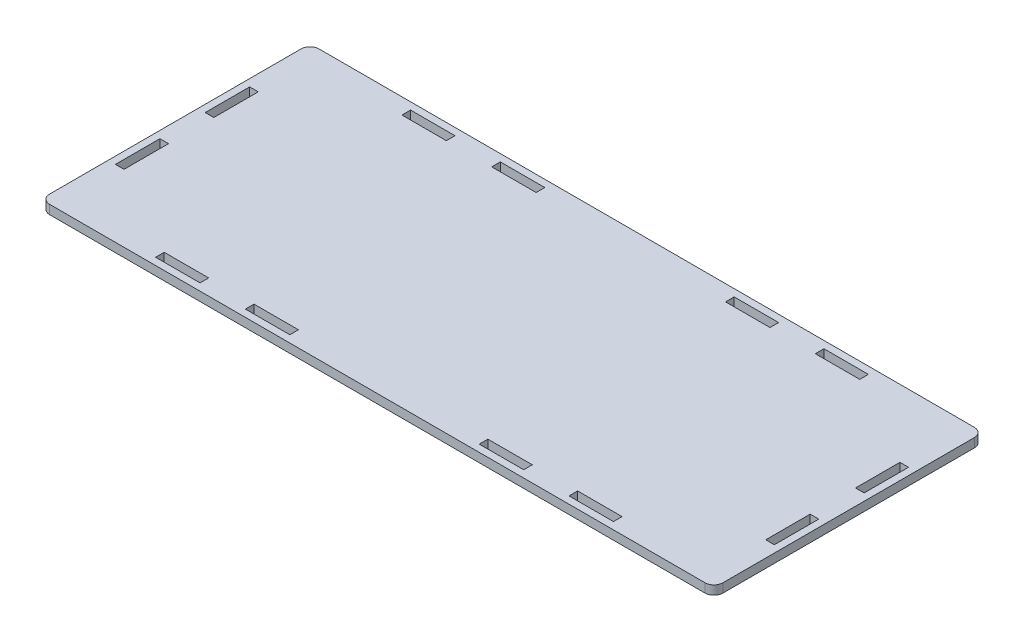
SolidWorks part; units mm, degrees
ref_plane "Front Plane" through (0, 0, 0) normal (0, 0, 1) x (1, 0, 0)
ref_plane "Top Plane" through (0, 0, 0) normal (0, 1, 0) x (1, 0, 0)
ref_plane "Right Plane" through (0, 0, 0) normal (1, 0, 0) x (0, 0, -1)
sketch "Sketch1" plane through (0, 0, 0) normal (0, 1, 0) x (1, 0, 0)
  line L1 (0, 0) -> (750, 0)
  line L2 (0, 0) -> (0, 300)
  line L3 (0, 300) -> (750, 300)
  line L4 (750, 0) -> (750, 300)
  dimension "D1" = 750
  dimension "D2" = 300
extrude "Boss-Extrude1" add sketch "Sketch1" along normal blind 10 contours L3 L4 L1 L2
sketch "Sketch2" plane through (0, 10, 0) normal (0, 1, 0) x (1, 0, 0)
  line L0 (375, 300) -> (375, 0) construction
  line L1 (0, 300) -> (750, 300) construction
  line L2 (0, 0) -> (750, 0) construction
  line L3 (375, 150) -> (585, 150) construction
  line L4 (585, 80) -> (585, 220) construction
  line L5 (655, 80) -> (585, 80) construction
  line L6 (0, 0) -> (0, 300) construction
  circle A0 centre (375, 80) radius 43.75
  circle A1 centre (515, 80) radius 43.75
  circle A2 centre (655, 80) radius 43.75
  circle A3 centre (235, 80) radius 43.75
  circle A4 centre (95, 80) radius 43.75
  circle A5 centre (165, 220) radius 43.75
  circle A6 centre (305, 220) radius 43.75
  circle A7 centre (445, 220) radius 43.75
  circle A8 centre (585, 220) radius 43.75
  circle A9 centre (60, 240) radius 15
  circle A10 centre (60, 190) radius 14.75
  dimension "D1" = 140
  dimension "D2" = 140
  dimension "D3" = 140
  dimension "D4" = 140
  dimension "D5" = 140
  dimension "D6" = 140
  dimension "D7" = 140
  dimension "D8" = 140
  dimension "D9" = 87.5
  dimension "D10" = 29.5
  dimension "D11" = 30
  dimension "D12" = 50
  dimension "D13" = 60
  dimension "D14" = 60
extrude "Cut-Extrude2" [suppressed] cut sketch "Sketch2" against normal through all
sketch "Sketch4" plane through (0, 10, 0) normal (0, 1, 0) x (1, 0, 0)
  line L0 (17.6, 124.75) -> (8, 124.75)
  line L1 (17.6, 224.75) -> (8, 224.75)
  line L2 (17.6, 224.75) -> (17.6, 175.25)
  line L3 (17.6, 175.25) -> (8, 175.25)
  line L4 (8, 224.75) -> (8, 175.25)
  line L5 (17.6, 124.75) -> (17.6, 75.25)
  line L6 (17.6, 75.25) -> (8, 75.25)
  line L7 (8, 124.75) -> (8, 75.25)
  line L8 (0, 150) -> (272.3767, 150) construction
  line L9 (0, 0) -> (0, 300) construction
  line L10 (375, 0) -> (375, 191.3353) construction
  line L11 (0, 0) -> (750, 0) construction
  line L12 (732.4, 175.25) -> (742, 175.25)
  line L13 (732.4, 224.75) -> (732.4, 175.25)
  line L14 (732.4, 224.75) -> (742, 224.75)
  line L15 (742, 124.75) -> (742, 75.25)
  line L16 (732.4, 75.25) -> (742, 75.25)
  line L17 (732.4, 124.75) -> (742, 124.75)
  line L18 (732.4, 124.75) -> (732.4, 75.25)
  line L19 (742, 224.75) -> (742, 175.25)
  line L20 (0, 300) -> (750, 300) construction
  line L21 (120, 282.4) -> (169.5, 282.4)
  line L22 (120, 282.4) -> (120, 292)
  line L23 (120, 292) -> (169.5, 292)
  line L24 (169.5, 282.4) -> (169.5, 292)
  line L25 (220, 292) -> (269.5, 292)
  line L26 (220, 292) -> (220, 282.4)
  line L27 (220, 282.4) -> (269.5, 282.4)
  line L28 (269.5, 292) -> (269.5, 282.4)
  line L29 (480.5, 292) -> (480.5, 282.4)
  line L30 (530, 282.4) -> (480.5, 282.4)
  line L31 (530, 292) -> (530, 282.4)
  line L32 (530, 292) -> (480.5, 292)
  line L33 (580.5, 282.4) -> (580.5, 292)
  line L34 (630, 292) -> (580.5, 292)
  line L35 (630, 282.4) -> (630, 292)
  line L36 (630, 282.4) -> (580.5, 282.4)
  line L37 (630, 17.6) -> (580.5, 17.6)
  line L38 (630, 17.6) -> (630, 8)
  line L39 (630, 8) -> (580.5, 8)
  line L40 (580.5, 17.6) -> (580.5, 8)
  line L41 (530, 8) -> (480.5, 8)
  line L42 (530, 8) -> (530, 17.6)
  line L43 (530, 17.6) -> (480.5, 17.6)
  line L44 (480.5, 8) -> (480.5, 17.6)
  line L45 (269.5, 8) -> (269.5, 17.6)
  line L46 (220, 17.6) -> (269.5, 17.6)
  line L47 (220, 8) -> (220, 17.6)
  line L48 (220, 8) -> (269.5, 8)
  line L49 (169.5, 17.6) -> (169.5, 8)
  line L50 (120, 8) -> (169.5, 8)
  line L51 (120, 17.6) -> (120, 8)
  line L52 (120, 17.6) -> (169.5, 17.6)
  point P8 (8, 100)
  point P9 (8, 200)
  point P22 (742, 200)
  point P27 (742, 100)
  point P36 (244.75, 292)
  point P37 (144.75, 292)
  point P40 (120, 287.2)
  point P49 (605.25, 292)
  point P50 (505.25, 292)
  point P67 (505.25, 8)
  point P68 (605.25, 8)
  point P69 (144.75, 8)
  point P70 (244.75, 8)
  dimension "D1" = 9.6
  dimension "D2" = 49.5
  dimension "D3" = 100
  dimension "D4" = 8
  dimension "D5" = 100
  dimension "D6" = 8
  dimension "D7" = 120
extrude "Cut-Extrude3" cut sketch "Sketch4" against normal through all
fillet "Fillet1" radius 10 4 edges at (750, 5, -300) (750, 5, 0) (0, 5, 0) (0, 5, -300)
